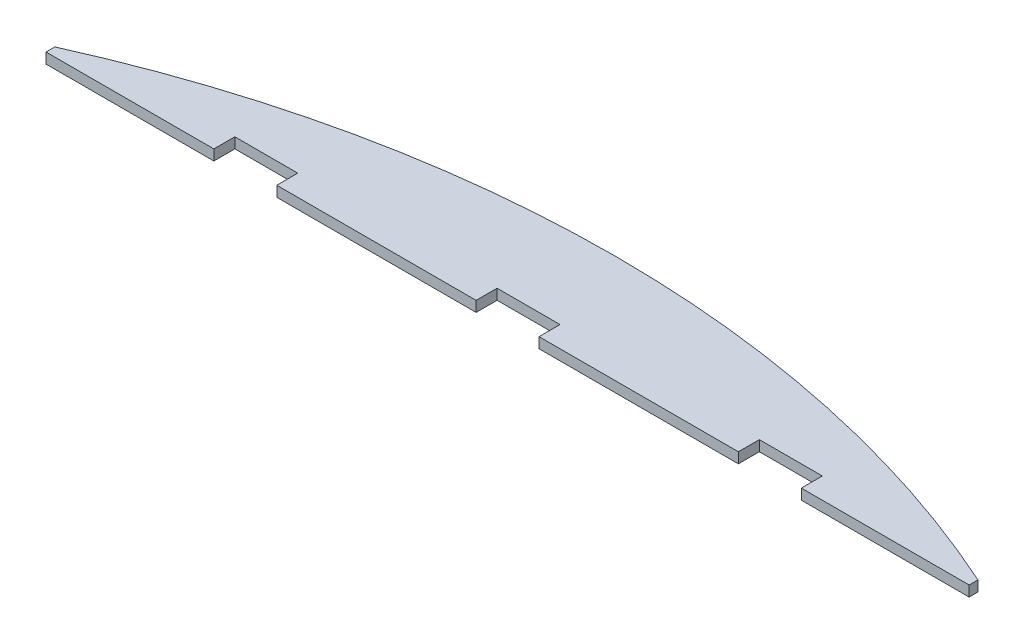
SolidWorks part; units mm, degrees
ref_plane "前视基准面" through (0, 0, 0) normal (0, 0, 1) x (1, 0, 0)
ref_plane "上视基准面" through (0, 0, 0) normal (0, 1, 0) x (1, 0, 0)
ref_plane "右视基准面" through (0, 0, 0) normal (1, 0, 0) x (0, 0, -1)
other "Configuration Table"
sketch "草图1" plane through (0, 0, 0) normal (0, 1, 0) x (1, 0, 0)
  line L0 (-30, -3) -> (-44, -3)
  line L1 (-30, 3) -> (30, 3) construction
  line L2 (-30, 3) -> (-30, -3) construction
  line L3 (-30, -3) -> (30, -3)
  line L4 (30, 3) -> (30, -3) construction
  line L5 (-30, 3) -> (30, -3) construction
  line L6 (-30, -3) -> (30, 3) construction
  line L7 (30, -3) -> (44, -3)
  line L9 (-44, 25.6817) -> (44, 25.6817) construction
  line L10 (-44, -2.1583) -> (-44, -3)
  line L11 (-44, -25.6817) -> (44, -25.6817) construction
  line L12 (44, -2.1583) -> (44, -3)
  line L13 (-44, 25.6817) -> (44, -25.6817) construction
  line L14 (-44, -25.6817) -> (44, 25.6817) construction
  arc A0 (44, -2.1583) -> (-44, -2.1583) centre (0, -100) ccw
  point P0 (0, 0)
  point P7 (0, 0)
  dimension "D1" = 6
  dimension "D2" = 100
  dimension "D3" = 60
  dimension "D4" = 88
extrude "凸台-拉伸1" add sketch "草图1" along normal blind 1
sketch "草图2" plane through (0, 0, 0) normal (0, -1, 0) x (1, 0, 0)
  line L0 (-44, 3) -> (44, 3) construction
  line L1 (-3, 5) -> (3, 5)
  line L2 (-3, 5) -> (-3, 1)
  line L3 (-3, 1) -> (3, 1)
  line L4 (3, 5) -> (3, 1)
  line L5 (-3, 5) -> (3, 1) construction
  line L6 (-3, 1) -> (3, 5) construction
  line L7 (22, 5) -> (28, 5)
  line L8 (22, 5) -> (22, 1)
  line L9 (28, 5) -> (28, 1)
  line L10 (22, 1) -> (28, 1)
  line L11 (-3, 5) -> (22, 5) construction
  line L12 (-28, 5) -> (-22, 5)
  line L13 (-28, 5) -> (-28, 1)
  line L14 (-28, 1) -> (-22, 1)
  line L15 (-22, 5) -> (-22, 1)
  line L16 (-3, 5) -> (-28, 5) construction
  point P0 (0, 3)
  dimension "D1" = 6
  dimension "D2" = 4
  dimension "D4" = 25
  dimension "D6" = 25
  dimension "D3" = 2
  dimension "D5" = 2
extrude "切除-拉伸1" cut sketch "草图2" against normal through all
